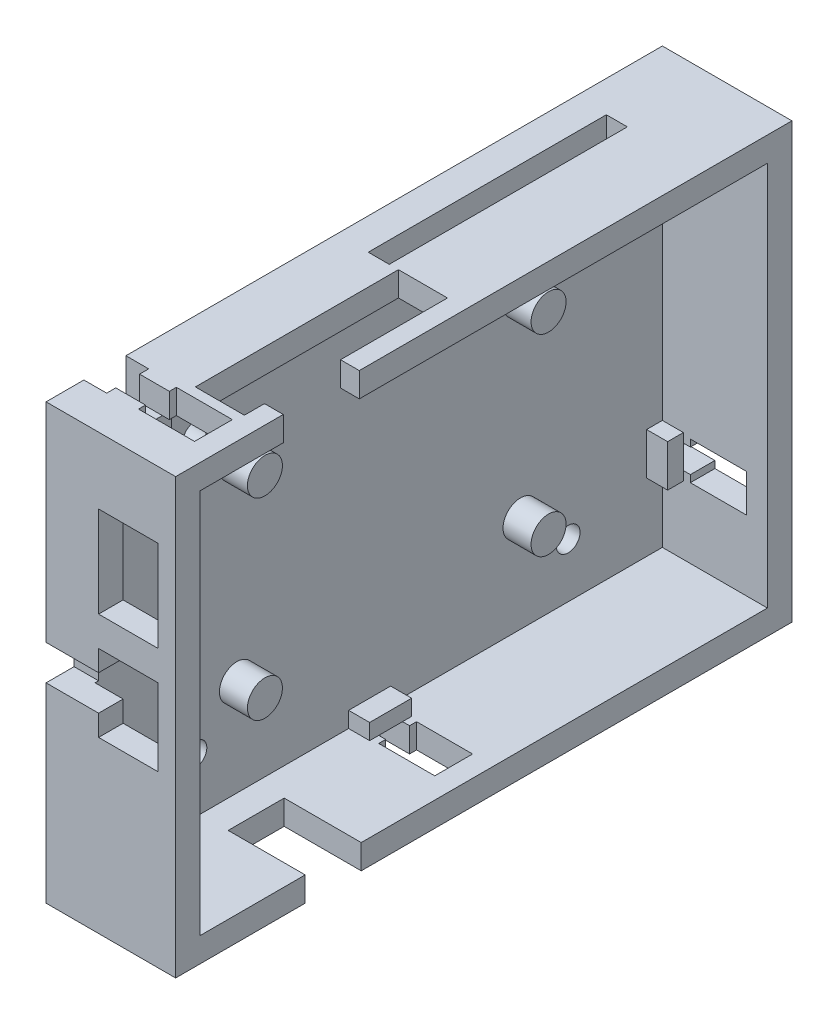
SolidWorks part; units mm, degrees
ref_plane "前视基准面" through (0, 0, 0) normal (0, 0, 1) x (1, 0, 0)
ref_plane "上视基准面" through (0, 0, 0) normal (0, 1, 0) x (1, 0, 0)
ref_plane "右视基准面" through (0, 0, 0) normal (1, 0, 0) x (0, 0, -1)
sketch "草图1" plane through (0, 0, 0) normal (1, 0, 0) x (0, 0, -1)
  line L5 (0, 0) -> (-3.5, 0) construction
  line L6 (0, 0) -> (0, -3.5) construction
  line L7 (0, -3.5) -> (-3.5, -3.5) construction
  line L8 (-3.5, 0) -> (-3.5, -3.5) construction
  line L9 (-3.5, -3.5) -> (84.5, -3.5)
  line L10 (-3.5, -3.5) -> (-3.5, 58.5)
  line L11 (-3.5, 58.5) -> (84.5, 58.5)
  line L12 (84.5, -3.5) -> (84.5, 58.5)
  dimension "D3" = 3.5
  dimension "D4" = 3.5
  dimension "D5" = 88
  dimension "D6" = 62
extrude "凸台-拉伸1" add sketch "草图1" along normal blind 3.5 contours L10 L9 L12 L11
sketch "草图2" plane through (3.5, 0, 0) normal (1, 0, 0) x (0, 0, -1)
  line L1 (0, 0) -> (81, 0)
  line L2 (0, 0) -> (0, 55)
  line L3 (0, 55) -> (81, 55)
  line L4 (81, 0) -> (81, 55)
  line L5 (-3.5, -3.5) -> (84.5, -3.5)
  line L6 (-3.5, -3.5) -> (-3.5, 58.5)
  line L7 (-3.5, 58.5) -> (84.5, 58.5)
  line L8 (84.5, -3.5) -> (84.5, 58.5)
  dimension "D1" = 81
  dimension "D2" = 55
extrude "凸台-拉伸2" add sketch "草图2" along normal blind 15
sketch "草图3" plane through (3.5, 0, 0) normal (1, 0, 0) x (0, 0, -1)
  line L0 (0, 55) -> (81, 0) construction
  line L1 (0, 0) -> (81, 55) construction
  line L2 (40.5, 27.5) -> (0, 55) construction
  line L3 (40.5, 0) -> (40.5, 55) construction
  line L4 (0, 0) -> (81, 0) construction
  line L5 (81, 55) -> (0, 55) construction
  line L6 (0, 27.5) -> (81, 27.5) construction
  line L7 (0, 55) -> (0, 0) construction
  line L8 (81, 0) -> (81, 55) construction
  circle A0 centre (20.25, 41.25) radius 2.5
  circle A1 centre (60.75, 41.25) radius 2.5
  circle A2 centre (60.75, 13.75) radius 2.5
  circle A3 centre (20.25, 13.75) radius 2.5
extrude "凸台-拉伸3" add sketch "草图3" along normal blind 4
sketch "草图4" plane through (0, 58.5, 0) normal (0, 1, 0) x (1, 0, 0)
  line L0 (6.8166, 38) -> (6.8166, 9)
  line L1 (0, 84.5) -> (7.5, 84.5) construction
  line L2 (0, 84.5) -> (0, 72) construction
  line L3 (0, 72) -> (7.5, 72) construction
  line L4 (7.5, 84.5) -> (7.5, 72) construction
  line L5 (7.5, 72) -> (4.5, 72)
  line L6 (7.5, 72) -> (7.5, 38)
  line L7 (7.5, 38) -> (4.5, 38)
  line L8 (4.5, 72) -> (4.5, 38)
  line L9 (0, 0) -> (0, 3.2)
  line L14 (6.8166, 9) -> (15.8166, 9)
  line L15 (6.8166, 9) -> (6.8166, 38)
  line L16 (6.8166, 38) -> (15.8166, 38)
  line L17 (15.8166, 9) -> (15.8166, 38)
  line L18 (0, -3.5) -> (0, 84.5) construction
  line L19 (0, 3.2) -> (7.5, 3.2)
  line L20 (7.5, 3.2) -> (7.5, 2.2)
  line L21 (7.5, 2.2) -> (15.5, 2.2)
  line L22 (15.5, 2.2) -> (15.5, 7.6)
  line L23 (15.5, 7.6) -> (7.5, 7.6)
  line L24 (7.5, 7.6) -> (7.5, 6.6)
  line L25 (7.5, 6.6) -> (0, 6.6)
  line L26 (0, 6.6) -> (0, 3.2)
  line L27 (18.5, 84.5) -> (18.5, -3.5) construction
  line L28 (15.8166, 11.8692) -> (18.5, 11.8692)
  line L29 (15.8166, 11.8692) -> (15.8166, 22.7264)
  line L30 (15.8166, 22.7264) -> (18.5, 22.7264)
  line L31 (18.5, 11.8692) -> (18.5, 22.7264)
  dimension "D1" = 7.5
  dimension "D2" = 12.5
  dimension "D3" = 3
  dimension "D4" = 34
  dimension "D5" = 29
  dimension "D6" = 29
  dimension "D7" = 9
  dimension "D8" = 3.2
  dimension "D9" = 3.4
  dimension "D10" = 29
  dimension "D11" = 9
extrude "切除-拉伸2" cut sketch "草图4" against normal blind 3.5 contours L5 L8 L7 L6 | L14 L17 L16 L7 L0 | L19 L20 L21 L22 L23 L24 L25 L26 | L29 L28 L31 L30
sketch "草图7" plane through (0, 0, 3.5) normal (0, 0, 1) x (1, 0, 0)
  line L0 (0, 58.5) -> (7.5, 58.5) construction
  line L1 (18.5, 58.5) -> (0, 58.5) construction
  line L2 (7.5, 58.5) -> (7.5, 49) construction
  line L3 (7.5, 58.5) -> (7.5, 31.75)
  line L4 (7.5, 49) -> (16, 49)
  line L5 (7.5, 49) -> (7.5, 36)
  line L6 (7.5, 36) -> (16, 36)
  line L7 (16, 49) -> (16, 36)
  line L9 (7.5, 31.75) -> (16, 31.75)
  line L10 (7.5, 31.75) -> (7.5, 20.75)
  line L11 (7.5, 20.75) -> (16, 20.75)
  line L12 (16, 31.75) -> (16, 20.75)
  line L17 (0, -3.5) -> (0, 58.5) construction
  line L18 (7.5, 26.25) -> (0, 26.25)
  line L19 (7.5, 26.25) -> (7.5, 28.75)
  line L20 (7.5, 28.75) -> (0, 28.75)
  line L21 (0, 26.25) -> (0, 28.75)
  line L23 (7.5, 26.25) -> (0, 26.25)
  line L24 (7.5, 26.25) -> (7.5, 23.75)
  line L25 (7.5, 23.75) -> (0, 23.75)
  line L26 (0, 26.25) -> (0, 23.75)
  dimension "D8" = 2.5
  dimension "D1" = 7.5
  dimension "D2" = 9.5
  dimension "D3" = 8.5
  dimension "D4" = 13
  dimension "D5" = 26.75
  dimension "D6" = 11
  dimension "D7" = 8.5
  dimension "D9" = 2.5
extrude "切除-拉伸3" cut sketch "草图7" against normal blind 4 contours L12 L9 L10 L11 | L7 L4 L3 L6 | L19 L20 L21 L18 | L24 L23 L26 L25
sketch "草图8" plane through (0, -3.5, 0) normal (0, -1, 0) x (1, 0, 0)
  line L0 (0, 0) -> (7.5, 0) construction
  line L1 (7.5, 0) -> (7.5, -15) construction
  line L2 (7.5, 0) -> (7.5, -36.5) construction
  line L3 (7.5, -15) -> (19.5, -15)
  line L4 (7.5, -15) -> (7.5, -23)
  line L5 (7.5, -23) -> (19.5, -23)
  line L6 (19.5, -15) -> (19.5, -23)
  line L7 (7.5, -36.5) -> (15.5, -36.5)
  line L8 (15.5, -36.5) -> (15.5, -41.9)
  line L9 (15.5, -41.9) -> (7.5, -41.9)
  line L10 (7.5, -41.9) -> (7.5, -40.9)
  line L11 (7.5, -40.9) -> (0, -40.9)
  line L12 (0, 3.5) -> (0, -84.5) construction
  line L13 (0, -40.9) -> (0, -37.5)
  line L14 (0, -37.5) -> (7.5, -37.5)
  line L15 (7.5, -37.5) -> (7.5, -36.5)
  dimension "D1" = 7.5
  dimension "D2" = 15
  dimension "D3" = 8
  dimension "D4" = 12
  dimension "D5" = 36.5
  dimension "D6" = 5.4
  dimension "D7" = 1
  dimension "D8" = 1
extrude "切除-拉伸4" cut sketch "草图8" against normal blind 3.5 contours L4 L3 L6 L5 | L15 L7 L8 L9 L10 L11 L13 L14
sketch "草图9" plane through (0, 0, -84.5) normal (0, 0, -1) x (-1, 0, 0)
  line L0 (0, 0) -> (0, 11)
  line L1 (0, -3.5) -> (0, 58.5) construction
  line L2 (0, 11) -> (-7.5, 11)
  line L3 (-7.5, 11) -> (-7.5, 10)
  line L4 (-7.5, 10) -> (-15.5, 10)
  line L5 (-15.5, 10) -> (-15.5, 15.4)
  line L6 (-15.5, 15.4) -> (-7.5, 15.4)
  line L7 (-7.5, 15.4) -> (-7.5, 14.4)
  line L8 (-7.5, 14.4) -> (0, 14.4)
  line L9 (0, 14.4) -> (0, 11)
  line M9 (0, -3.5) -> (0, 58.5)
  dimension "D1" = 11
  dimension "D2" = 3.4
  dimension "D3" = 1
  dimension "D4" = 1
  dimension "D5" = 7.5
  dimension "D6" = 7.5
  dimension "D7" = 8
extrude "切除-拉伸5" cut sketch "草图9" against normal blind 3.5 contours L8 L7 L6 L5 L4 L3 L2 M9
sketch "草图10" plane through (3.5, 0, 0) normal (1, 0, 0) x (0, 0, -1)
  line L0 (0, 27.5) -> (81, 27.5) construction
  line L2 (81, 0) -> (81, 55) construction
  line L3 (40.9, 56.082) -> (40.9, 0) construction
  line L6 (20.25, 41.25) -> (14.25, 41.25) construction
  line L7 (20.25, 41.25) -> (20.25, 47.25) construction
  line L8 (20.25, 47.25) -> (14.25, 47.25) construction
  line L9 (14.25, 41.25) -> (14.25, 47.25) construction
  circle A0 centre (14.25, 47.25) radius 1.7
  circle A1 centre (14.25, 7.75) radius 1.7
  circle A2 centre (67.55, 7.75) radius 1.7
  point P2 (51.8632, 55)
  point P3 (-31.2279, 32.1757)
  dimension "D3" = 3.4
  dimension "D1" = 6
  dimension "D2" = 6
extrude "切除-拉伸6" cut sketch "草图10" against normal blind 3.5
sketch "草图11" plane through (3.5, 0, 0) normal (1, 0, 0) x (0, 0, -1)
  line L0 (4.9, 55) -> (4.9, 52.75)
  line L1 (6.6, 55) -> (3.2, 55) construction
  line L2 (4.9, 52.75) -> (1.9, 52.75)
  line L3 (81, 11) -> (81, 14.4) construction
  line L4 (1.9, 52.75) -> (7.9, 52.75)
  line L5 (1.9, 52.75) -> (1.9, 55)
  line L6 (1.9, 55) -> (7.9, 55)
  line L7 (7.9, 52.75) -> (7.9, 55)
  line L8 (81, 12.7) -> (78.75, 12.7) construction
  line L9 (81, 12.7) -> (81, 15.7) construction
  line L10 (81, 15.7) -> (78.75, 15.7) construction
  line L11 (78.75, 12.7) -> (78.75, 15.7) construction
  line L12 (81, 0) -> (81, 11) construction
  line L13 (78.75, 15.7) -> (81, 15.7)
  line L14 (78.75, 15.7) -> (78.75, 9.7)
  line L15 (78.75, 9.7) -> (81, 9.7)
  line L16 (81, 15.7) -> (81, 9.7)
  line L17 (37.5, 0) -> (40.9, 0) construction
  line L18 (39.2, 0) -> (42.2, 0) construction
  line L19 (39.2, 0) -> (39.2, 2.25) construction
  line L20 (39.2, 2.25) -> (42.2, 2.25) construction
  line L21 (42.2, 0) -> (42.2, 2.25) construction
  line L23 (42.2, 2.25) -> (36.2, 2.25)
  line L24 (42.2, 2.25) -> (42.2, 0)
  line L25 (42.2, 0) -> (36.2, 0)
  line L26 (36.2, 2.25) -> (36.2, 0)
  line M25 (0, 0) -> (37.5, 0)
  line M26 (37.5, 0) -> (40.9, 0)
  line M27 (40.9, 0) -> (81, 0)
  line M28 (81, 0) -> (81, 11)
  line M29 (81, 11) -> (81, 14.4)
  line M30 (81, 14.4) -> (81, 55)
  line M31 (81, 55) -> (6.6, 55)
  line M32 (6.6, 55) -> (3.2, 55)
  line M33 (3.2, 55) -> (0, 55)
  dimension "D1" = 2.25
  dimension "D2" = 3
  dimension "D3" = 6
  dimension "D4" = 2.25
  dimension "D5" = 3
  dimension "D6" = 2.25
  dimension "D7" = 6
  dimension "D8" = 3
  dimension "D9" = 2.25
  dimension "D10" = 6
  dimension "D11" = 2.25
extrude "凸台-拉伸4" add sketch "草图11" along normal blind 3 contours L23 L26 L24 M25 M26 M27 | L14 L15 L13 M28 M29 M30 | L5 L2 L0 M32 M33 | L4 L7 L0 M31 M32
sketch "草图12" plane through (0, 0, 0) normal (-1, 0, 0) x (0, 0, 1)
  line L0 (-6.6, 55) -> (-3.2, 55) construction
  line L1 (-4.9, 55) -> (-1.9, 55) construction
  line L2 (-4.9, 55) -> (-4.9, 52.75) construction
  line L3 (-4.9, 52.75) -> (-1.9, 52.75) construction
  line L4 (-1.9, 55) -> (-1.9, 52.75) construction
  line L5 (-6.6, 58.5) -> (-84.5, 58.5) construction
  line L6 (-1.9, 52.75) -> (-7.9, 52.75)
  line L7 (-1.9, 52.75) -> (-1.9, 58.5)
  line L8 (-1.9, 58.5) -> (-7.9, 58.5)
  line L9 (-7.9, 52.75) -> (-7.9, 58.5)
  line L15 (-40.9, 0) -> (-37.5, 0) construction
  line L16 (-39.2, 0) -> (-36.2, 0) construction
  line L17 (-39.2, 0) -> (-39.2, 2.25) construction
  line L18 (-39.2, 2.25) -> (-36.2, 2.25) construction
  line L19 (-36.2, 0) -> (-36.2, 2.25) construction
  line L20 (-81, 10) -> (-81, 15.4) construction
  line L21 (-36.2, 2.25) -> (-42.2, 2.25)
  line L22 (-36.2, 2.25) -> (-36.2, -3.5)
  line L23 (-36.2, -3.5) -> (-42.2, -3.5)
  line L24 (-42.2, 2.25) -> (-42.2, -3.5)
  line L25 (-81, 12.7) -> (-78.75, 12.7) construction
  line L26 (-81, 12.7) -> (-81, 9.7) construction
  line L27 (-81, 9.7) -> (-78.75, 9.7) construction
  line L28 (-78.75, 12.7) -> (-78.75, 9.7) construction
  line L29 (-84.5, 14.4) -> (-84.5, 58.5) construction
  line L30 (-78.75, 9.7) -> (-84.5, 9.7)
  line L31 (-78.75, 9.7) -> (-78.75, 15.7)
  line L32 (-78.75, 15.7) -> (-84.5, 15.7)
  line L33 (-84.5, 9.7) -> (-84.5, 15.7)
  dimension "D1" = 3
  dimension "D2" = 2.25
  dimension "D3" = 6
  dimension "D4" = 3
  dimension "D5" = 2.25
  dimension "D6" = 6
  dimension "D7" = 3
  dimension "D8" = 2.25
  dimension "D9" = 6
extrude "切除-拉伸7" cut sketch "草图12" against normal blind 3.25
sketch "草图13" plane through (6.8166, 0, 0) normal (1, 0, 0) x (0, 0, -1)
  line L0 (38, 55) -> (38, 58.5) construction
  line L1 (9, 58.5) -> (38, 58.5)
  line L2 (9, 58.5) -> (9, 55)
  line L3 (9, 55) -> (38, 55)
  line L4 (38, 58.5) -> (38, 55)
extrude "凸台-拉伸5" add sketch "草图13" along normal blind 2
